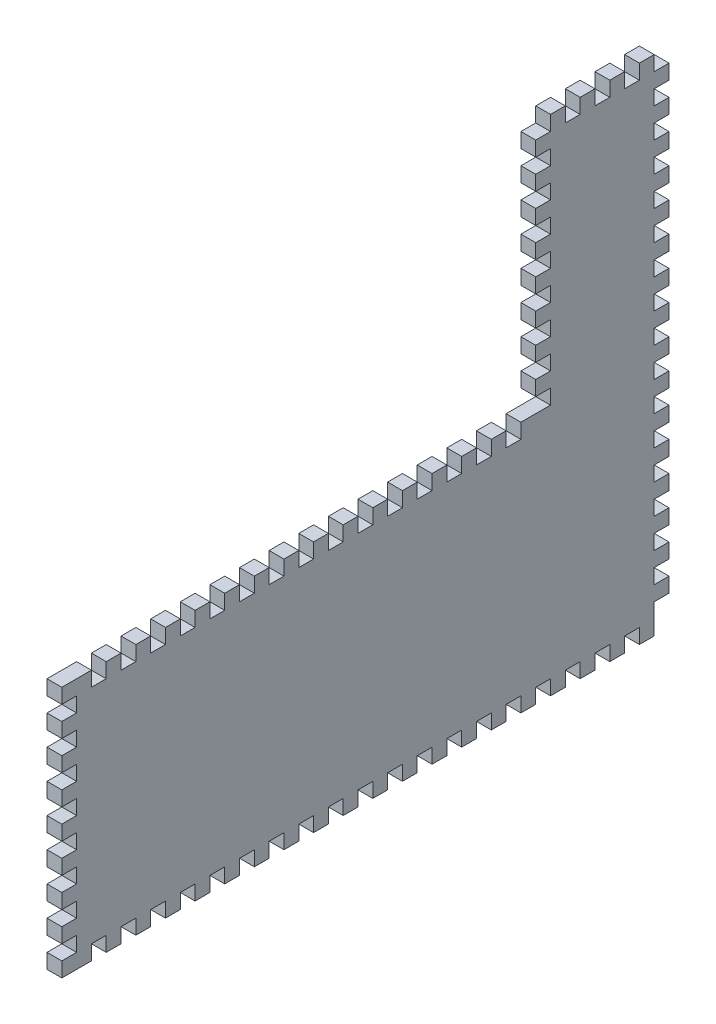
SolidWorks part; units mm, degrees
material "Malleable Cast Iron"
ref_plane "Front Plane" through (0, 0, 0) normal (0, 0, 1) x (1, 0, 0)
ref_plane "Top Plane" through (0, 0, 0) normal (0, 1, 0) x (1, 0, 0)
ref_plane "Right Plane" through (0, 0, 0) normal (1, 0, 0) x (0, 0, -1)
sketch "Sketch1" plane through (0, 0, 0) normal (1, 0, 0) x (0, 0, -1)
  line L1 (-130.175, -53.975) -> (130.175, -53.975)
  line L2 (-130.175, -53.975) -> (-130.175, 53.975)
  line L3 (-130.175, 53.975) -> (73.025, 53.975)
  line L4 (130.175, -53.975) -> (130.175, 53.975)
  line L5 (-130.175, -53.975) -> (130.175, 53.975) construction
  line L6 (-130.175, 53.975) -> (130.175, -53.975) construction
  line L8 (130.175, 53.975) -> (130.175, 161.925)
  line L9 (130.175, 161.925) -> (73.025, 161.925)
  line L10 (73.025, 53.975) -> (73.025, 161.925)
  point P0 (0, 0)
  dimension "D1" = 107.95
  dimension "D2" = 260.35
  dimension "D3" = 107.95
  dimension "D4" = 57.15
  dimension "D5" = 107.95
extrude "Boss-Extrude1" add sketch "Sketch1" along normal blind 6.35
sketch "Sketch2" plane through (6.35, 0, 0) normal (1, 0, 0) x (0, 0, -1)
  line L0 (-130.175, 53.975) -> (-130.175, -53.975) construction
  line L2 (-130.175, -47.625) -> (-123.825, -47.625)
  line L3 (-130.175, -47.625) -> (-130.175, -41.275)
  line L4 (-130.175, -41.275) -> (-123.825, -41.275)
  line L5 (-123.825, -47.625) -> (-123.825, -41.275)
  dimension "D1" = 6.35
  dimension "D2" = 6.35
  dimension "D3" = 6.35
extrude "Cut-Extrude1" cut sketch "Sketch2" against normal through all
pattern_linear "LPattern1" count 8 spacing 12.7 along (0, 1, 0) of "Cut-Extrude1"
sketch "Sketch3" plane through (6.35, 0, 0) normal (1, 0, 0) x (0, 0, -1)
  line L0 (-130.175, -53.975) -> (130.175, -53.975) construction
  line L1 (-117.475, -53.975) -> (-111.125, -53.975)
  line L2 (-117.475, -53.975) -> (-117.475, -47.625)
  line L3 (-117.475, -47.625) -> (-111.125, -47.625)
  line L4 (-111.125, -53.975) -> (-111.125, -47.625)
  dimension "D1" = 12.7
  dimension "D2" = 6.35
  dimension "D3" = 6.35
extrude "Cut-Extrude2" cut sketch "Sketch3" against normal blind 6.35
pattern_linear "LPattern2" count 20 spacing 12.7 along (0, 0, -1) of "Cut-Extrude2"
sketch "Sketch4" plane through (6.35, 0, 0) normal (1, 0, 0) x (0, 0, -1)
  line L0 (73.025, 53.975) -> (-130.175, 53.975) construction
  line L1 (-117.475, 53.975) -> (-111.125, 53.975)
  line L2 (-117.475, 53.975) -> (-117.475, 47.625)
  line L3 (-117.475, 47.625) -> (-111.125, 47.625)
  line L4 (-111.125, 53.975) -> (-111.125, 47.625)
  dimension "D1" = 12.7
  dimension "D2" = 6.35
  dimension "D3" = 6.35
extrude "Cut-Extrude3" cut sketch "Sketch4" against normal through all
pattern_linear "LPattern3" count 15 spacing 12.7 along (0, 0, -1) of "Cut-Extrude3"
sketch "Sketch5" plane through (6.35, 0, 0) normal (1, 0, 0) x (0, 0, -1)
  line L1 (130.175, 161.925) -> (123.825, 161.925)
  line L2 (130.175, 161.925) -> (130.175, 155.575)
  line L3 (130.175, 155.575) -> (123.825, 155.575)
  line L4 (123.825, 161.925) -> (123.825, 155.575)
  dimension "D1" = 6.35
  dimension "D2" = 6.35
extrude "Cut-Extrude4" cut sketch "Sketch5" against normal through all
pattern_linear "LPattern4" count 17 spacing 12.7 along (0, -1, 0) of "Cut-Extrude4"
sketch "Sketch6" plane through (6.35, 0, 0) normal (1, 0, 0) x (0, 0, -1)
  line L1 (73.025, 161.925) -> (79.375, 161.925)
  line L2 (73.025, 161.925) -> (73.025, 155.575)
  line L3 (73.025, 155.575) -> (79.375, 155.575)
  line L4 (79.375, 161.925) -> (79.375, 155.575)
  dimension "D1" = 6.35
  dimension "D2" = 6.35
extrude "Cut-Extrude5" cut sketch "Sketch6" against normal through all
pattern_linear "LPattern5" count 9 spacing 12.7 along (0, -1, 0) of "Cut-Extrude5"
pattern_linear "LPattern6" count 4 spacing 12.7 along (0, 0, -1) of "Cut-Extrude5"
